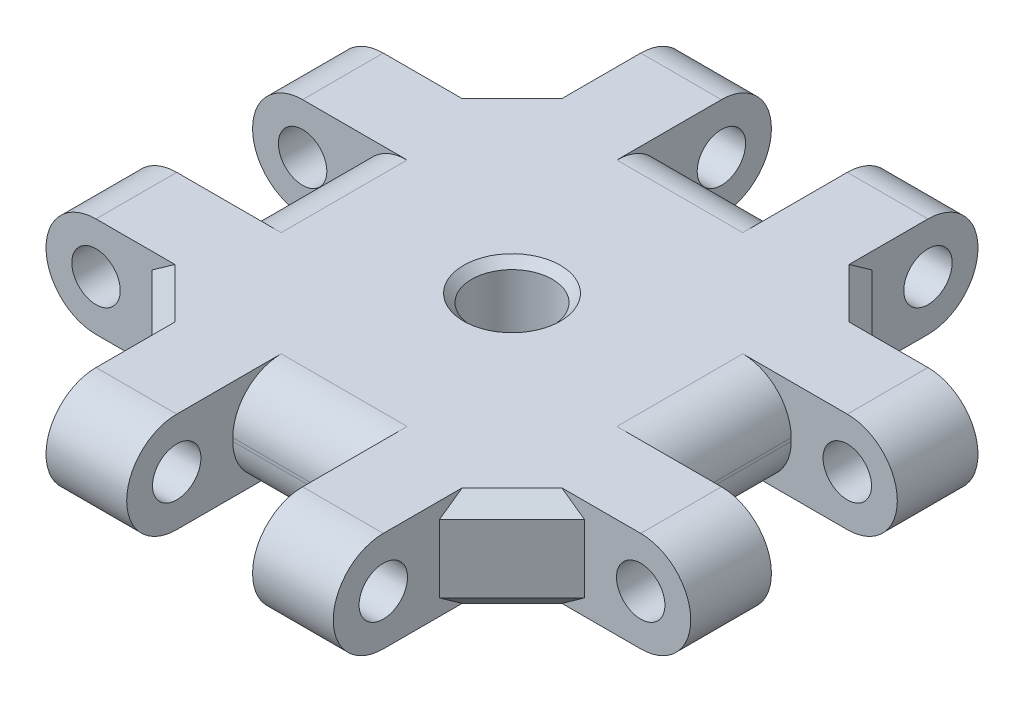
SolidWorks part; units mm, degrees
ref_plane "Front Plane" through (0, 0, 0) normal (0, 0, 1) x (1, 0, 0)
ref_plane "Top Plane" through (0, 0, 0) normal (0, 1, 0) x (1, 0, 0)
ref_plane "Right Plane" through (0, 0, 0) normal (1, 0, 0) x (0, 0, -1)
sketch "Sketch1" plane through (0, 0, 0) normal (0, 1, 0) x (1, 0, 0)
  line L0 (-8.9, -13.4) -> (-8.9, -20.35)
  line L1 (-13.4, -13.4) -> (13.4, -13.4) construction
  line L2 (-13.4, -13.4) -> (-13.4, 13.4) construction
  line L3 (-13.4, 13.4) -> (13.4, 13.4) construction
  line L4 (13.4, -13.4) -> (13.4, 13.4) construction
  line L5 (-13.4, -13.4) -> (13.4, 13.4) construction
  line L6 (-13.4, 13.4) -> (13.4, -13.4) construction
  line L7 (-8.9, -20.35) -> (-3.9, -20.35)
  line L8 (-3.9, -20.35) -> (-3.9, -13.4)
  line L9 (-3.9, -13.4) -> (3.9, -13.4)
  line L10 (3.9, -13.4) -> (3.9, -20.35)
  line L11 (3.9, -20.35) -> (8.9, -20.35)
  line L12 (8.9, -20.35) -> (8.9, -13.4)
  line L13 (-8.9, -13.4) -> (-13.4, -13.4) construction
  line L14 (-13.4, 8.9) -> (-20.35, 8.9)
  line L15 (-20.35, 8.9) -> (-20.35, 3.9)
  line L16 (-20.35, 3.9) -> (-13.4, 3.9)
  line L17 (-13.4, 3.9) -> (-13.4, -3.9)
  line L18 (-13.4, -3.9) -> (-20.35, -3.9)
  line L19 (-20.35, -3.9) -> (-20.35, -8.9)
  line L20 (-20.35, -8.9) -> (-13.4, -8.9)
  line L21 (8.9, 13.4) -> (8.9, 20.35)
  line L22 (8.9, 20.35) -> (3.9, 20.35)
  line L23 (3.9, 20.35) -> (3.9, 13.4)
  line L24 (3.9, 13.4) -> (-3.9, 13.4)
  line L25 (-3.9, 13.4) -> (-3.9, 20.35)
  line L26 (-3.9, 20.35) -> (-8.9, 20.35)
  line L27 (-8.9, 20.35) -> (-8.9, 13.4)
  line L28 (13.4, -8.9) -> (20.35, -8.9)
  line L29 (20.35, -8.9) -> (20.35, -3.9)
  line L30 (20.35, -3.9) -> (13.4, -3.9)
  line L31 (13.4, -3.9) -> (13.4, 3.9)
  line L32 (13.4, 3.9) -> (20.35, 3.9)
  line L33 (20.35, 3.9) -> (20.35, 8.9)
  line L34 (20.35, 8.9) -> (13.4, 8.9)
  line L35 (-13.4, 8.9) -> (-8.9, 13.4)
  line L36 (8.9, 13.4) -> (13.4, 8.9)
  line L37 (13.4, -8.9) -> (8.9, -13.4)
  line L38 (-8.9, -13.4) -> (-13.4, -8.9)
  circle A0 centre (0, 0) radius 2.5
  point P0 (0, 0)
  point P17 (0, 0)
  point P26 (0, 0)
  point P35 (0, 0)
  point P44 (0, 0)
  dimension "D9" = 5
  dimension "D1" = 6.364
  dimension "D2" = 5
  dimension "D3" = 5
  dimension "D4" = 7.8
  dimension "D5" = 6.95
  dimension "D6" = 6.95
  dimension "D7" = 4.5
  dimension "D8" = 4
extrude "Boss-Extrude1" add sketch "Sketch1" along normal mid plane 6.2
sketch "Sketch2" plane through (-8.9, 0, 0) normal (-1, 0, 0) x (0, 0, 1)
  line L0 (13.4, 3.1) -> (20.35, -3.1) construction
  line L1 (20.35, 3.1) -> (13.4, -3.1) construction
  line L2 (13.4, 3.1) -> (20.35, 3.1) construction
  line L3 (13.4, -3.1) -> (20.35, -3.1) construction
  line L4 (16.875, 3.1) -> (20.35, 3.1)
  line L5 (20.35, 3.1) -> (20.35, -3.1)
  line L6 (20.35, -3.1) -> (16.875, -3.1)
  circle A0 centre (16.875, 0) radius 1.5
  arc A1 (16.875, 3.1) -> (16.875, -3.1) centre (16.875, 0) cw
  dimension "D1" = 3
extrude "Cut-Extrude1" cut sketch "Sketch2" against normal through all both and the other way through all
pattern_circular "CirPattern1" count 4 every 90 about axis through (0, 3.1, 0) along (0, 1, 0) of "Cut-Extrude1"
fillet "Fillet1" radius 3 8 edges at (0, -3.1, 13.4) (-13.4, -3.1, 0) (13.4, -3.1, 0) (0, -3.1, -13.4) (-13.4, 3.1, 0) (0, 3.1, -13.4) (13.4, 3.1, 0) (0, 3.1, 13.4)
chamfer "Chamfer1" distance 1 angle 45 8 edges at (11.15, -3.1, 11.15) (11.15, 3.1, 11.15) (11.15, -3.1, -11.15) (11.15, 3.1, -11.15) (-11.15, -3.1, -11.15) (-11.15, 3.1, -11.15) (-11.15, -3.1, 11.15) (-11.15, 3.1, 11.15)
chamfer "Chamfer3" distance 0.5 angle 45 2 edges at (0, -3.1, 2.5) (0, 3.1, 2.5)
